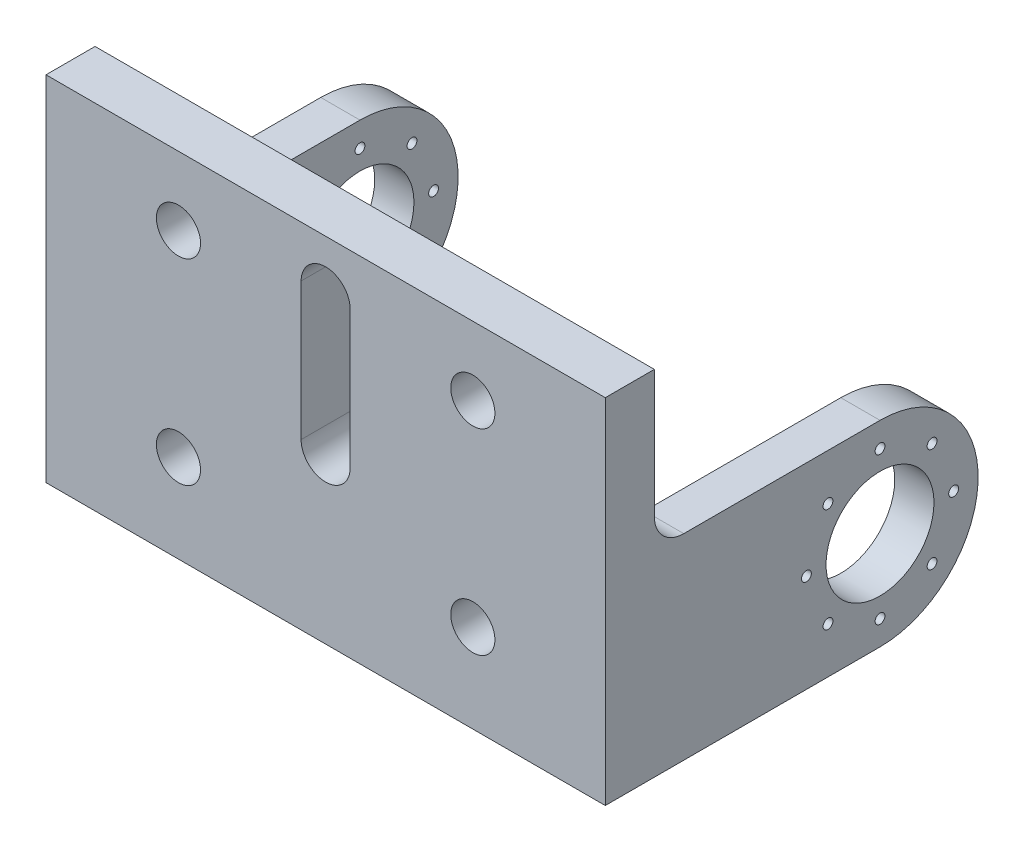
SolidWorks part; units mm, degrees
ref_plane "Front Plane" through (0, 0, 0) normal (0, 0, 1) x (1, 0, 0)
ref_plane "Top Plane" through (0, 0, 0) normal (0, 1, 0) x (1, 0, 0)
ref_plane "Right Plane" through (0, 0, 0) normal (1, 0, 0) x (0, 0, -1)
sketch "Sketch1" plane through (0, 0, 0) normal (0, 0, 1) x (1, 0, 0)
  line L1 (-28.5, -18) -> (28.5, -18)
  line L2 (-28.5, -18) -> (-28.5, 18)
  line L3 (-28.5, 18) -> (28.5, 18)
  line L4 (28.5, -18) -> (28.5, 18)
  line L5 (-28.5, -18) -> (28.5, 18) construction
  line L6 (-28.5, 18) -> (28.5, -18) construction
  point P0 (0, 0)
  dimension "D1" = 57
  dimension "D2" = 36
extrude "Boss-Extrude1" add sketch "Sketch1" against normal blind 5
sketch "Sketch3" plane through (-28.5, 0, 0) normal (-1, 0, 0) x (0, 0, 1)
  line L1 (-5, -18) -> (-28, -18)
  line L2 (-5, -18) -> (-5, 2)
  line L3 (-5, 2) -> (-28, 2)
  line L4 (-28, -18) -> (-28, 2)
  dimension "D1" = 23
  dimension "D2" = 20
extrude "Boss-Extrude3" add sketch "Sketch3" against normal blind 4
sketch "Sketch4" plane through (-28.5, 0, 0) normal (-1, 0, 0) x (0, 0, 1)
  line L6 (0, -18) -> (0, 18)
  line L7 (0, 18) -> (-5, 18)
  line L8 (-5, 18) -> (-5, 2)
  line L9 (-5, 2) -> (-28, 2)
  line L10 (-28, 2) -> (-28, -18)
  line L11 (-28, -18) -> (0, -18)
  line L16 (-28, 2) -> (-28, -18)
  arc A0 (-28, 2) -> (-28, -18) centre (-28, -8) ccw
  dimension "D1" = 0
extrude "Boss-Extrude4" add sketch "Sketch4" against normal blind 4
ref_plane "Plane1" through (0, 0, 0) normal (1, 0, 0) x (0, 0, -1)
mirror "Mirror1" about plane through (0, 0, 0) normal (1, 0, 0) of "Boss-Extrude3", "Boss-Extrude4"
fillet "Fillet1" radius 3 2 edges at (26.5, 2, -5)
sketch "Sketch5" plane through (0, 0, 0) normal (0, 0, 1) x (1, 0, 0)
  line L0 (0, -1.2) -> (0, 12.8) construction
  line L1 (0, -19.8) -> (0, 19.8) construction
  line L2 (-2.5, -1.2) -> (-2.5, 12.8)
  line L3 (2.5, -1.2) -> (2.5, 12.8)
  line L4 (28.5, 18) -> (-28.5, 18) construction
  arc A0 (-2.5, -1.2) -> (2.5, -1.2) centre (0, -1.2) ccw
  arc A1 (2.5, 12.8) -> (-2.5, 12.8) centre (0, 12.8) ccw
  point P5 (0, 5.8)
  dimension "D1" = 2.5
  dimension "D3" = 5.2
  dimension "D2" = 14
extrude "Cut-Extrude1" cut sketch "Sketch5" against normal up to next
sketch "Sketch6" plane through (28.5, 0, 0) normal (1, 0, 0) x (0, 0, -1)
  circle A0 centre (28, -8) radius 5.5
  dimension "D1" = 11
extrude "Cut-Extrude2" cut sketch "Sketch6" against normal through all
sketch "Sketch7" plane through (28.5, 0, 0) normal (1, 0, 0) x (0, 0, -1)
  line L0 (28, -8) -> (21.9295, -8) construction
  circle A0 centre (20.5, -8) radius 0.5
  circle A3 centre (28, -8) radius 5.5 construction
  dimension "D1" = 1
  dimension "D2" = 7.5
extrude "Cut-Extrude3" cut sketch "Sketch7" against normal through all
pattern_circular "CirPattern1" count 8 over 360 about axis through (0, -8, -28) along (1, 0, 0) of "Cut-Extrude3"
sketch "Sketch8" plane through (0, 0, 0) normal (0, 0, 1) x (1, 0, 0)
  line L0 (28.5, 18) -> (-28.5, 18) construction
  line L1 (0, -19.8) -> (0, 19.8) construction
  circle A0 centre (-15, 11) radius 2.25
  dimension "D3" = 4.5
  dimension "D1" = 7
  dimension "D2" = 15
extrude "Cut-Extrude4" cut sketch "Sketch8" against normal up to next (5 mm away)
pattern_linear "LPattern1" count 2 spacing 30 along (1, 0, 0) count 2 spacing 20 along (0, -1, 0) of "Cut-Extrude4"
